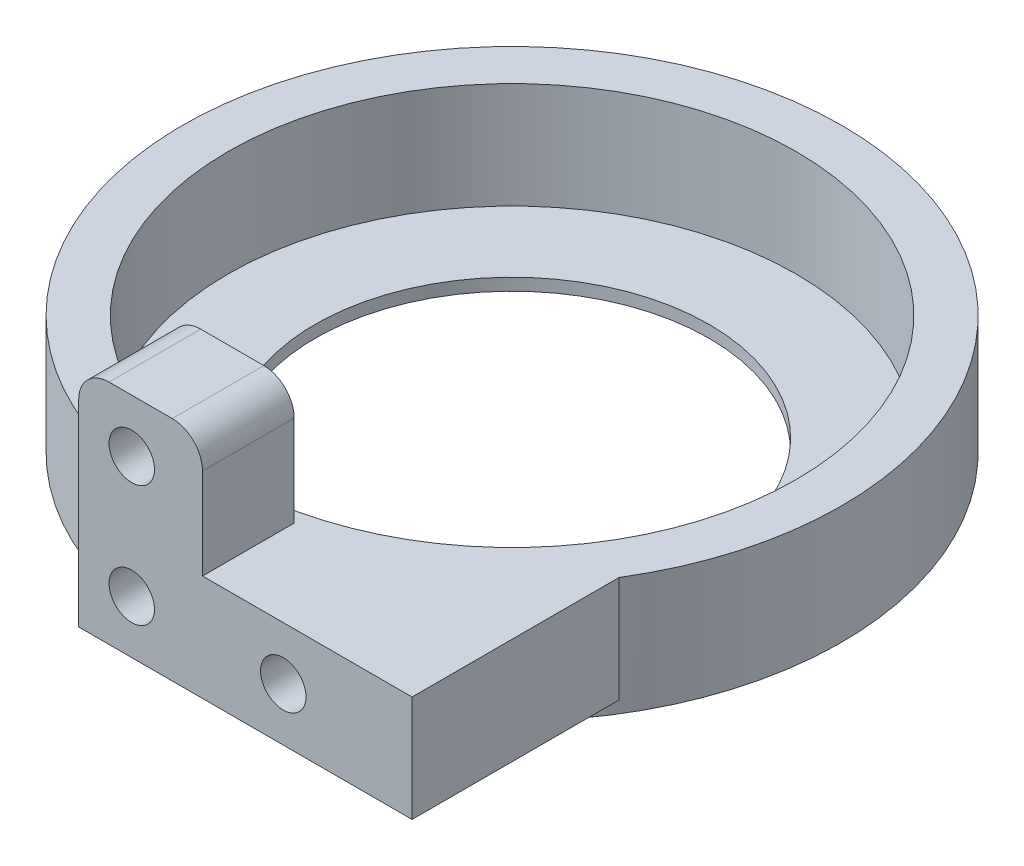
SolidWorks part; units mm, degrees
ref_plane "Front Plane" through (0, 0, 0) normal (0, 0, 1) x (1, 0, 0)
ref_plane "Top Plane" through (0, 0, 0) normal (0, 1, 0) x (1, 0, 0)
ref_plane "Right Plane" through (0, 0, 0) normal (1, 0, 0) x (0, 0, -1)
sketch "Sketch1" plane through (0, 0, 0) normal (0, 1, 0) x (1, 0, 0)
  line L0 (0, -20.1) -> (0, -25.1) construction
  line L1 (3.5, -25.1) -> (-3.5, -25.1)
  line L2 (-3.5, -25.1) -> (-3.5, -21.4665)
  line L3 (3.5, -25.1) -> (3.5, -21.4665)
  circle A0 centre (0, 0) radius 18.75
  arc A1 (3.5, -21.4665) -> (-3.5, -21.4665) centre (0, 0) ccw
  circle A3 centre (0, 0) radius 21.75 construction
  point P11 (19.2217, 5.8767)
  dimension "D1" = 3
  dimension "D3" = 3.5
  dimension "D2" = 5
extrude "Boss-Extrude1" add sketch "Sketch1" along normal blind 7 contours A1 L2 L1 L3 | A0
sketch "Sketch2" plane through (0, 0, 25.1) normal (0, 0, 1) x (1, 0, 0)
  line L0 (0, 7) -> (0, 0) construction
  line L1 (3.5, 7) -> (-3.5, 7) construction
  circle A0 centre (0, 3.5) radius 1.5
extrude "Cut-Extrude1" cut sketch "Sketch2" against normal blind 7
sketch "Sketch3" plane through (0, 0, 0) normal (0, -1, 0) x (1, 0, 0)
  circle A0 centre (0, 0) radius 21.75
  circle A1 centre (0, 0) radius 13
extrude "Boss-Extrude2" add sketch "Sketch3" along normal blind 0.8
sketch "Sketch5" plane through (3.5, 0, 0) normal (1, 0, 0) x (0, 0, -1)
  line L0 (-21.4665, 7) -> (-21.4665, 0) construction
  line L1 (-25.1, 7) -> (-21.4665, 7)
  line L2 (-25.1, 7) -> (-25.1, 0)
  line L3 (-25.1, 0) -> (-21.4665, 0)
  line L4 (-21.4665, 7) -> (-21.4665, 0)
extrude "Boss-Extrude4" add sketch "Sketch5" along normal blind 15
sketch "Sketch6" plane through (0, 7, 0) normal (0, 1, 0) x (1, 0, 0)
  line L0 (18.5, -25.1) -> (18.5, -11.4373)
  line L1 (18.5, -11.4373) -> (3.5, -21.4665)
  line L2 (3.5, -21.4665) -> (3.5, -25.1)
  line L3 (18.5, -25.1) -> (-3.5, -25.1) construction
  line L4 (3.5, -25.1) -> (18.5, -25.1)
  arc A0 (3.5, -21.4665) -> (-3.5, -21.4665) centre (0, 0) ccw construction
extrude "Boss-Extrude5" add sketch "Sketch6" against normal blind 7
sketch "Sketch7" plane through (0, 0, 25.1) normal (0, 0, 1) x (1, 0, 0)
  line L0 (0, 3.5) -> (10, 3.5) construction
  circle A0 centre (10, 3.5) radius 1.5
  dimension "D1" = 10
extrude "Cut-Extrude2" cut sketch "Sketch7" against normal blind 6
sketch "Sketch8" plane through (0, 7, 0) normal (0, 1, 0) x (1, 0, 0)
  line L1 (-3.5, -25.1) -> (4.6712, -25.1)
  line L2 (-3.5, -25.1) -> (-3.5, -19.0498)
  line L3 (-3.5, -19.0498) -> (4.6712, -19.0498)
  line L4 (4.6712, -25.1) -> (4.6712, -19.0498)
extrude "Boss-Extrude6" add sketch "Sketch8" along normal blind 8
sketch "Sketch9" plane through (0, 0, 25.1) normal (0, 0, 1) x (1, 0, 0)
  line L0 (0, 3.5) -> (0, 11.5) construction
  circle A0 centre (0, 11.5) radius 1.5
  dimension "D1" = 8
extrude "Cut-Extrude3" cut sketch "Sketch9" against normal blind 10
fillet "Fillet1" radius 2 2 edges at (-3.5, 15, 22.0749) (4.6712, 15, 22.0749)
